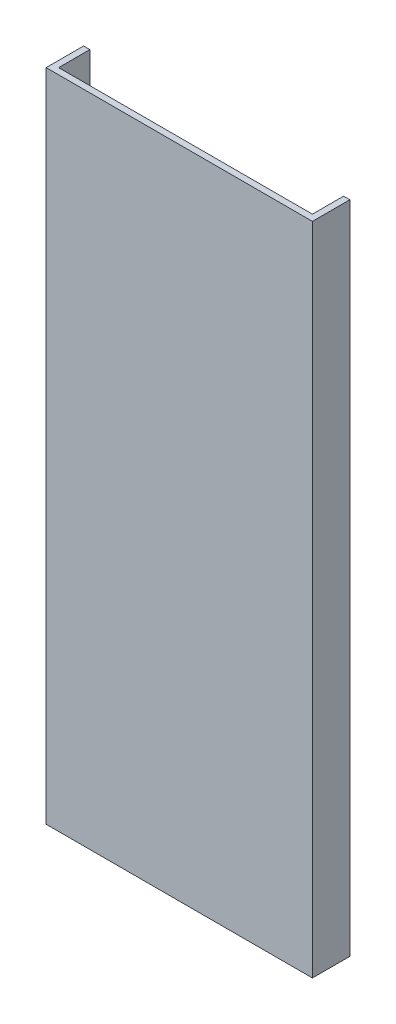
SolidWorks part; units mm, degrees
ref_plane "Front Plane" through (0, 0, 0) normal (0, 0, 1) x (1, 0, 0)
ref_plane "Top Plane" through (0, 0, 0) normal (0, 1, 0) x (1, 0, 0)
ref_plane "Right Plane" through (0, 0, 0) normal (1, 0, 0) x (0, 0, -1)
sketch "Sketch1" plane through (0, 0, 0) normal (0, 0, 1) x (1, 0, 0)
  line L1 (-64, 157.5) -> (64, 157.5)
  line L2 (-64, 157.5) -> (-64, -157.5)
  line L3 (-64, -157.5) -> (64, -157.5)
  line L4 (64, 157.5) -> (64, -157.5)
  line L5 (-64, 157.5) -> (64, -157.5) construction
  line L6 (-64, -157.5) -> (64, 157.5) construction
  point P0 (0, 0)
  dimension "D1" = 315
  dimension "D2" = 128
extrude "Boss-Extrude1" add sketch "Sketch1" along normal blind 3
sketch "Sketch2" plane through (0, 0, 0) normal (0, 0, -1) x (-1, 0, 0)
  line L0 (64, -157.5) -> (-64, -157.5) construction
  line L1 (-64, 157.5) -> (-61, 157.5)
  line L2 (-64, 157.5) -> (-64, -157.5)
  line L3 (-64, -157.5) -> (-61, -157.5)
  line L4 (-61, 157.5) -> (-61, -157.5)
  line L6 (64, -157.5) -> (-64, -157.5)
  line L7 (64, -157.5) -> (64, -154.5)
  line L8 (64, -154.5) -> (-64, -154.5)
  line L9 (-64, -157.5) -> (-64, -154.5)
  line L10 (64, 157.5) -> (61, 157.5)
  line L11 (64, 157.5) -> (64, -157.5)
  line L12 (64, -157.5) -> (61, -157.5)
  line L13 (61, 157.5) -> (61, -157.5)
  dimension "D1" = 3
  dimension "D2" = 3
  dimension "D3" = 3
extrude "Boss-Extrude3" add sketch "Sketch2" along normal blind 15 contours L11 L10 L13 L12 | L7 L6 L9 L8 | L2 L1 L4 L3
